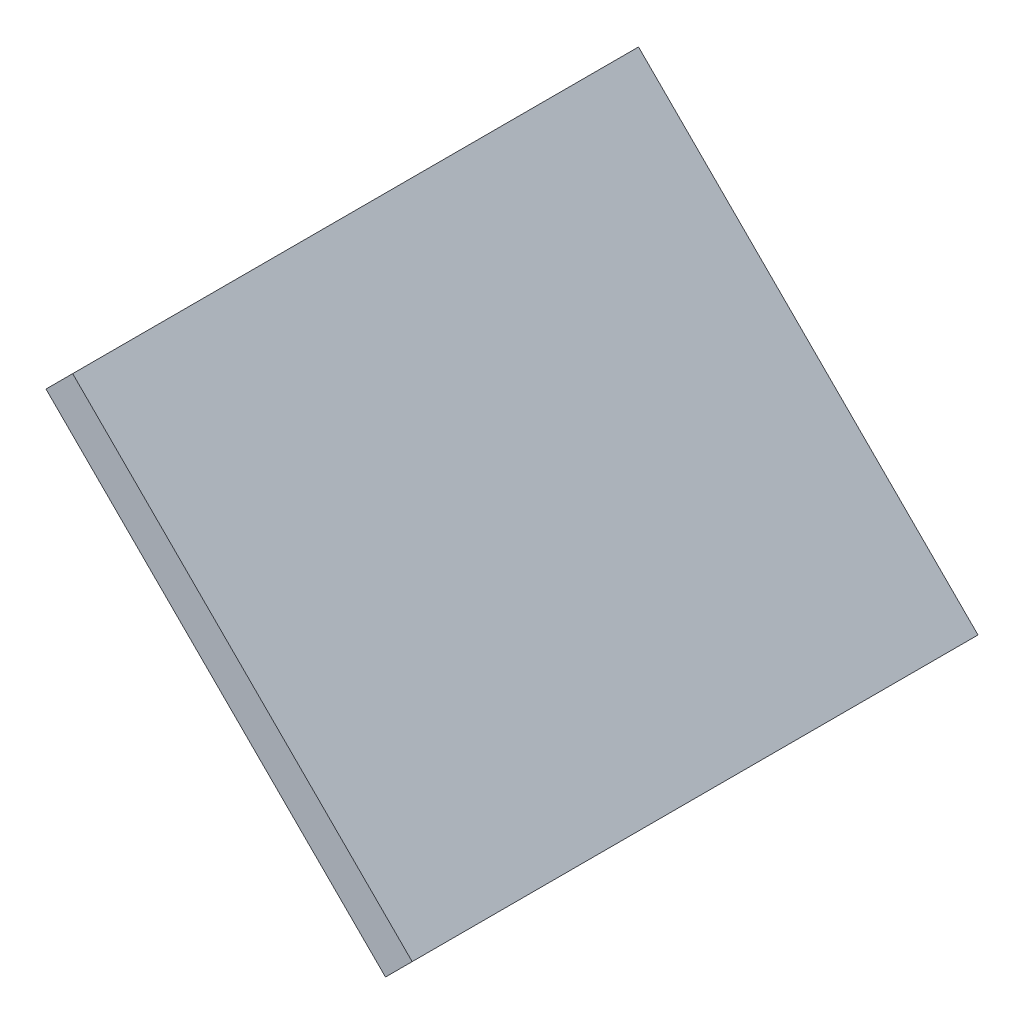
SolidWorks part; units mm, degrees
ref_plane "Front Plane" through (0, 0, 0) normal (0, 0, 1) x (1, 0, 0)
ref_plane "Top Plane" through (0, 0, 0) normal (0, 1, 0) x (1, 0, 0)
ref_plane "Right Plane" through (0, 0, 0) normal (1, 0, 0) x (0, 0, -1)
sketch "Sketch1" plane through (0, 0, 0) normal (0, 0, 1) x (1, 0, 0)
  line L0 (45, -45) -> (-45, 45)
  line L1 (55, 0) -> (-55, 0) construction
  point P4 (0, 0)
  dimension "D1" = 45
  dimension "D2" = 90
extrude "Extrude-Thin1" add sketch "Sketch1" along normal mid plane 150 thin thin type mid plane wall 10
